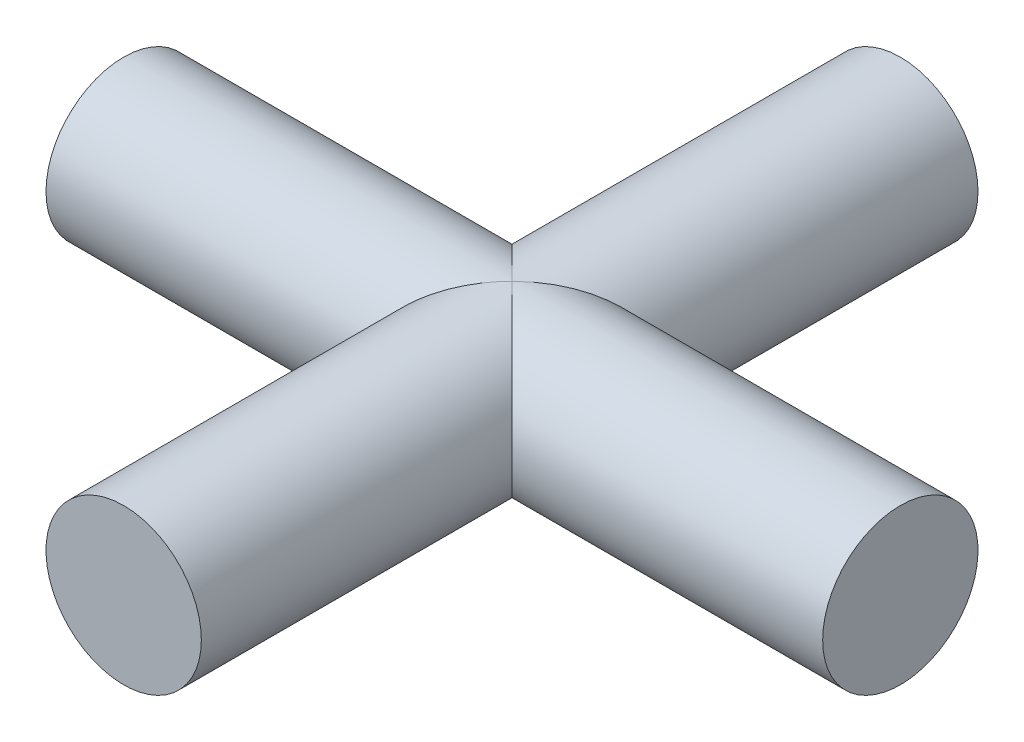
SolidWorks part; units mm, degrees
ref_plane "Front Plane" through (0, 0, 0) normal (0, 0, 1) x (1, 0, 0)
ref_plane "Top Plane" through (0, 0, 0) normal (0, 1, 0) x (1, 0, 0)
ref_plane "Right Plane" through (0, 0, 0) normal (1, 0, 0) x (0, 0, -1)
sketch "Sketch1" plane through (0, 0, 0) normal (0, 0, 1) x (1, 0, 0)
  circle A0 centre (0, 0) radius 6.35
  dimension "D1" = 12.7
extrude "Boss-Extrude1" add sketch "Sketch1" along normal blind 63.5
ref_plane "Plane1" through (0, 0, 31.75) normal (0, 0, 1) x (1, 0, 0)
sketch "Sketch2" plane through (0, 0, 31.75) normal (0, 0, 1) x (1, 0, 0)
  line L0 (0, 6.35) -> (0, -6.35) construction
pattern_circular "CirPattern1" count 2 over 90 about axis through (0, 6.35, 31.75) along (0, -1, 0) of "Boss-Extrude1"
